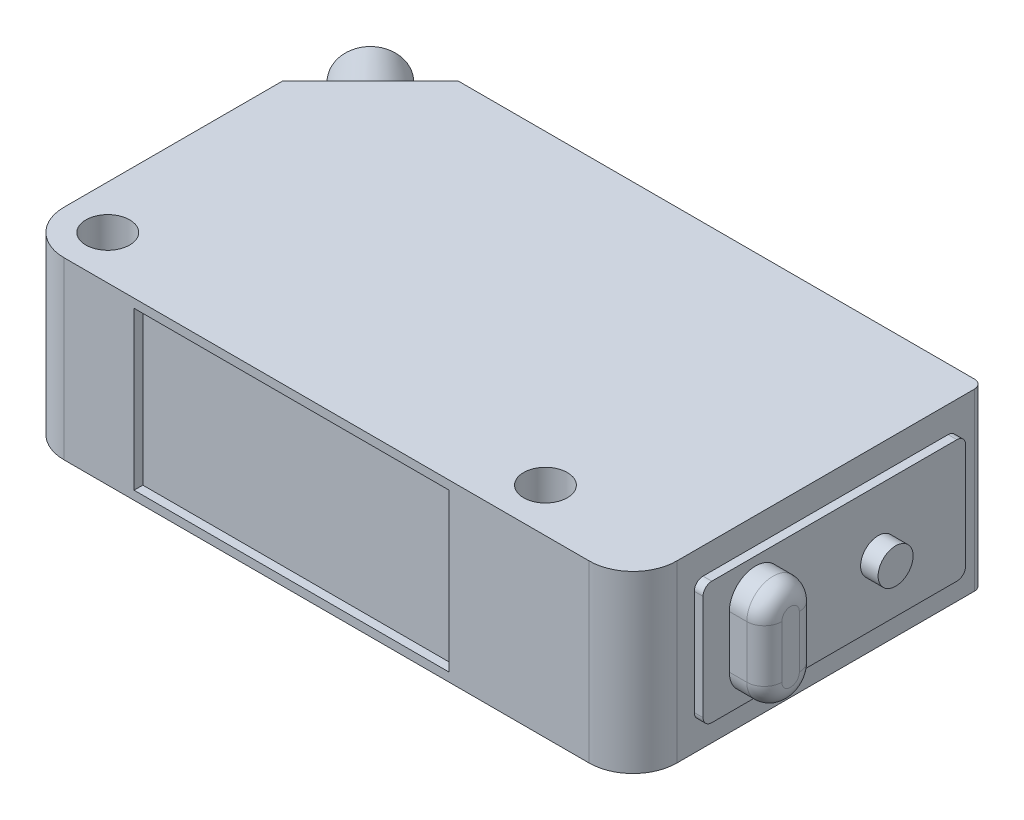
SolidWorks part; units mm, degrees
ref_plane "前视基准面" through (0, 0, 0) normal (0, 0, 1) x (1, 0, 0)
ref_plane "上视基准面" through (0, 0, 0) normal (0, 1, 0) x (1, 0, 0)
ref_plane "右视基准面" through (0, 0, 0) normal (1, 0, 0) x (0, 0, -1)
sketch "草图1" plane through (0, 0, 0) normal (0, 1, 0) x (1, 0, 0)
  line L0 (-12.5, 10) -> (-17.5, 5)
  line L1 (-12.5, 10) -> (17, 10)
  line L2 (-17.5, 5) -> (-17.5, -7.5)
  line L3 (-15, -10) -> (15, -10)
  line L4 (17.5, 9.5) -> (17.5, -7.5)
  line L5 (-17.5, 10) -> (17.5, -10) construction
  line L6 (-17.5, -10) -> (17.5, 10) construction
  arc A0 (17.5, -7.5) -> (15, -10) centre (15, -7.5) cw
  arc A1 (-15, -10) -> (-17.5, -7.5) centre (-15, -7.5) cw
  circle A2 centre (-15, -7.5) radius 0.5
  arc A3 (17.5, 9.5) -> (17, 10) centre (17, 9.5) ccw
  point P0 (0, 0)
  dimension "D3" = 2.5
  dimension "D4" = 1
  dimension "D6" = 0.5
  dimension "D1" = 35
  dimension "D2" = 20
extrude "凸台-拉伸1" add sketch "草图1" along normal blind 10
sketch "草图2" plane through (0, 10, 0) normal (0, 1, 0) x (1, 0, 0)
  line L0 (-15, -7.5) -> (10, -7.5) construction
  point P0 (-15, -7.5)
  point P5 (10, -7.5)
  dimension "D1" = 25
hole_wizard "M3 螺纹孔1" positions "3D草图1" profile "草图3" tap size "M3" standard "GB"
sketch3d "3D草图1"
  point P0 (10, 10, 7.5)
sketch "草图3" plane through (10, 10, 7.5) normal (1, 0, 0) x (0, 0, 1)
  line L0 (0, 0) -> (0, 19.2511)
  line L1 (0, 19.2511) -> (1.25, 18.5)
  line L2 (1.25, 18.5) -> (1.25, 0)
  line L5 (1.25, 0) -> (0, 0)
  line L10 (0, 19.2511) -> (-1.25, 18.5) construction
  line L11 (0, -6.35) -> (0, 107.95) construction
  dimension "螺纹孔钻头直径" = 2.5
  dimension "螺纹孔钻头深度" = 18.5
  dimension "导头角度" = 118
cosmetic thread "孔螺蚊线1" parameters "D1"=10, "D2"=3
sketch "草图4" plane through (0, 0, 0) normal (0, -1, 0) x (1, 0, 0)
  circle A0 centre (-15, 7.5) radius 0.5 construction
  circle A1 centre (-15, 7.5) radius 0.5
extrude "凸台-拉伸2" add sketch "草图4" against normal up to surface (10 mm away) up to face at (10, 10, 8.75)
hole_wizard "M3 螺纹孔2" positions "3D草图2" profile "草图5" tap size "M3" standard "GB"
sketch3d "3D草图2"
  point P0 (-15, 10, 7.5)
sketch "草图5" plane through (-15, 10, 7.5) normal (1, 0, 0) x (0, 0, 1)
  line L0 (0, 0) -> (0, 19.2511)
  line L1 (0, 19.2511) -> (1.25, 18.5)
  line L2 (1.25, 18.5) -> (1.25, 0)
  line L5 (1.25, 0) -> (0, 0)
  line L10 (0, 19.2511) -> (-1.25, 18.5) construction
  line L11 (0, -6.35) -> (0, 107.95) construction
  dimension "螺纹孔钻头直径" = 2.5
  dimension "螺纹孔钻头深度" = 18.5
  dimension "导头角度" = 118
cosmetic thread "孔螺蚊线2" parameters "D1"=10, "D2"=3
sketch "草图6" plane through (0, 0, 10) normal (0, 0, 1) x (1, 0, 0)
  line L0 (0, 0) -> (0, 10) construction
  line L1 (-15, 0) -> (15, 0) construction
  line L2 (-15, 10) -> (15, 10) construction
  line L3 (0, 5) -> (-2, 5) construction
  line L5 (-11, 9.5) -> (7, 9.5)
  line L6 (-11, 9.5) -> (-11, 0.5)
  line L7 (-11, 0.5) -> (7, 0.5)
  line L8 (7, 9.5) -> (7, 0.5)
  line L9 (-11, 9.5) -> (7, 0.5) construction
  line L10 (-11, 0.5) -> (7, 9.5) construction
  dimension "D1" = 2
  dimension "D2" = 18
  dimension "D3" = 9
extrude "切除-拉伸1" cut sketch "草图6" against normal blind 0.5
sketch "草图8" plane through (17.5, 0, 0) normal (1, 0, 0) x (0, 0, -1)
  line L0 (-7.5, 5) -> (9.5, 5) construction
  line L1 (-7.5, 10) -> (-7.5, 0) construction
  line L2 (9.5, 10) -> (9.5, 0) construction
  line L4 (8, 8.5) -> (-6, 8.5)
  line L5 (8.5, 8) -> (8.5, 2)
  line L6 (8, 1.5) -> (-6, 1.5)
  line L7 (-6.5, 8) -> (-6.5, 2)
  line L8 (8.5, 8.5) -> (-6.5, 1.5) construction
  line L9 (8.5, 1.5) -> (-6.5, 8.5) construction
  arc A0 (-6, 1.5) -> (-6.5, 2) centre (-6, 2) cw
  arc A1 (-6.5, 8) -> (-6, 8.5) centre (-6, 8) cw
  arc A2 (8, 1.5) -> (8.5, 2) centre (8, 2) ccw
  arc A3 (8.5, 8) -> (8, 8.5) centre (8, 8) ccw
  point P6 (1, 5)
  dimension "D3" = 0.5
  dimension "D1" = 7
  dimension "D2" = 15
extrude "凸台-拉伸3" add sketch "草图8" along normal blind 0.5
sketch "草图9" plane through (18, 0, 0) normal (1, 0, 0) x (0, 0, -1)
  line L0 (-6.5, 5) -> (-3.5, 5) construction
  line L1 (-6.5, 8) -> (-6.5, 2) construction
  line L2 (-3.5, 6.5) -> (-3.5, 3.5) construction
  line L3 (-2, 6.5) -> (-2, 3.5)
  line L4 (-5, 6.5) -> (-5, 3.5)
  arc A0 (-2, 6.5) -> (-5, 6.5) centre (-3.5, 6.5) ccw
  arc A1 (-5, 3.5) -> (-2, 3.5) centre (-3.5, 3.5) ccw
  point P6 (-3.5, 5)
  dimension "D1" = 3
extrude "凸台-拉伸4" add sketch "草图9" along normal blind 2
fillet "圆角4" radius 1 4 edges at (20, 5, 2) (20, 2, 3.5) (20, 5, 5) (20, 8, 3.5)
sketch "草图10" plane through (18, 0, 0) normal (1, 0, 0) x (0, 0, -1)
  line L0 (8.5, 5) -> (3.5, 5) construction
  line L1 (8.5, 2) -> (8.5, 8) construction
  circle A0 centre (3.5, 5) radius 1
  dimension "D2" = 2
  dimension "D1" = 5
extrude "凸台-拉伸5" add sketch "草图10" along normal blind 1
sketch "草图11" plane through (0, 0, -10) normal (0, 0, -1) x (-1, 0, 0)
  line L0 (-17, 5) -> (12.5, 5) construction
  line L1 (-17, 10) -> (-17, 0) construction
  line L2 (12.5, 10) -> (12.5, 0) construction
  line L4 (-8.25, 8.5) -> (3.75, 8.5)
  line L5 (-8.25, 8.5) -> (-8.25, 1.5)
  line L6 (-8.25, 1.5) -> (3.75, 1.5)
  line L7 (3.75, 8.5) -> (3.75, 1.5)
  line L8 (-8.25, 8.5) -> (3.75, 1.5) construction
  line L9 (-8.25, 1.5) -> (3.75, 8.5) construction
  point P6 (-2.25, 5)
  dimension "D1" = 12
  dimension "7" = 7
extrude "凸台-拉伸6" add sketch "草图11" along normal blind 0.1
sketch "草图12" plane through (0, 0, -10) normal (0, 0, -1) x (-1, 0, 0)
  line L0 (-8.25, 5) -> (-11.25, 5) construction
  line L1 (-8.25, 8.5) -> (-8.25, 1.5) construction
  line L2 (3.75, 5) -> (6.75, 5) construction
  line L3 (3.75, 1.5) -> (3.75, 8.5) construction
  circle A0 centre (-11.25, 5) radius 1
  circle A1 centre (6.75, 5) radius 1
  dimension "D3" = 2
  dimension "D4" = 2
  dimension "D1" = 3
  dimension "D2" = 3
extrude "凸台-拉伸7" add sketch "草图12" along normal blind 1
sketch "草图13" plane through (-11.25, 0, -11.25) normal (-0.7071, 0, -0.7071) x (-0.7071, 0, 0.7071)
  line L0 (1.7678, 5) -> (8.8388, 5) construction
  line L1 (1.7678, 10) -> (1.7678, 0) construction
  line L2 (8.8388, 10) -> (8.8388, 0) construction
  circle A0 centre (5.3033, 5) radius 1.75
  dimension "D1" = 3.5
extrude "凸台-拉伸8" add sketch "草图13" along normal blind 7
draft "拔模1" type of draft neutral plane draft angle 5 faces to draft 1 face at (-21.1872, 5, -11.2123) neutral plane through (-19.9497, 5, -12.4497) neutral plane normal (-0.7071, 0, -0.7071) parameters "D1"=5
